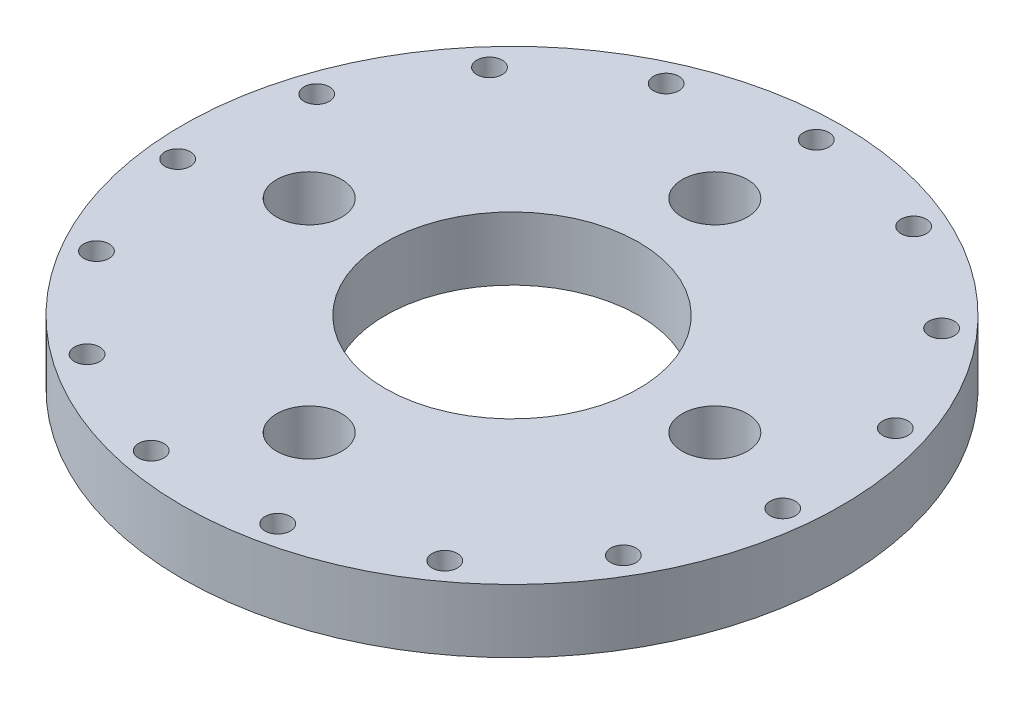
SolidWorks part; units mm, degrees
ref_plane "Front Plane" through (0, 0, 0) normal (0, 0, 1) x (1, 0, 0)
ref_plane "Top Plane" through (0, 0, 0) normal (0, 1, 0) x (1, 0, 0)
ref_plane "Right Plane" through (0, 0, 0) normal (1, 0, 0) x (0, 0, -1)
sketch "Sketch1" plane through (0, 0, 0) normal (0, 1, 0) x (1, 0, 0)
  circle A0 centre (0, 0) radius 16.51
  circle A1 centre (0, 0) radius 6.35
  dimension "D1" = 33.02
  dimension "D2" = 12.7
extrude "Boss-Extrude1" add sketch "Sketch1" along normal blind 3.175
hole_wizard "#4 Clearance Hole1" positions "Sketch3" profile "Sketch2" hole size "#4" standard "ANSI Inch"
sketch "Sketch3" plane through (0, 3.175, 0) normal (0, 1, 0) x (1, 0, 0)
  point P1 (0, 10.16)
  dimension "D1" = 10.16
sketch "Sketch2" plane through (0, 3.175, -10.16) normal (1, 0, 0) x (0, 0, 1)
  line L0 (0, 0) -> (0, 11.1406)
  line L1 (0, 11.1406) -> (1.6319, 10.16)
  line L2 (1.6319, 10.16) -> (1.6319, 0)
  line L5 (1.6319, 0) -> (0, 0)
  line L10 (0, 11.1406) -> (-1.6319, 10.16) construction
  line L11 (0, -6.35) -> (0, 107.95) construction
  dimension "Hole Dia." = 3.2639
  dimension "Hole Depth" = 10.16
  dimension "Drill Angle" = 118
pattern_circular "CirPattern1" count 4 every 90 about axis through (0, 0, 0) along (0, 1, 0) of "#4 Clearance Hole1"
sketch "Sketch4" plane through (0, 3.175, 0) normal (0, 1, 0) x (1, 0, 0)
  circle A0 centre (0, 15.24) radius 0.635
  dimension "D1" = 1.27
  dimension "D2" = 15.24
extrude "Cut-Extrude1" cut sketch "Sketch4" against normal blind 3.175
pattern_circular "CirPattern2" count 15 over 360 about axis through (0, 0, 0) along (0, 1, 0) of "Cut-Extrude1"
